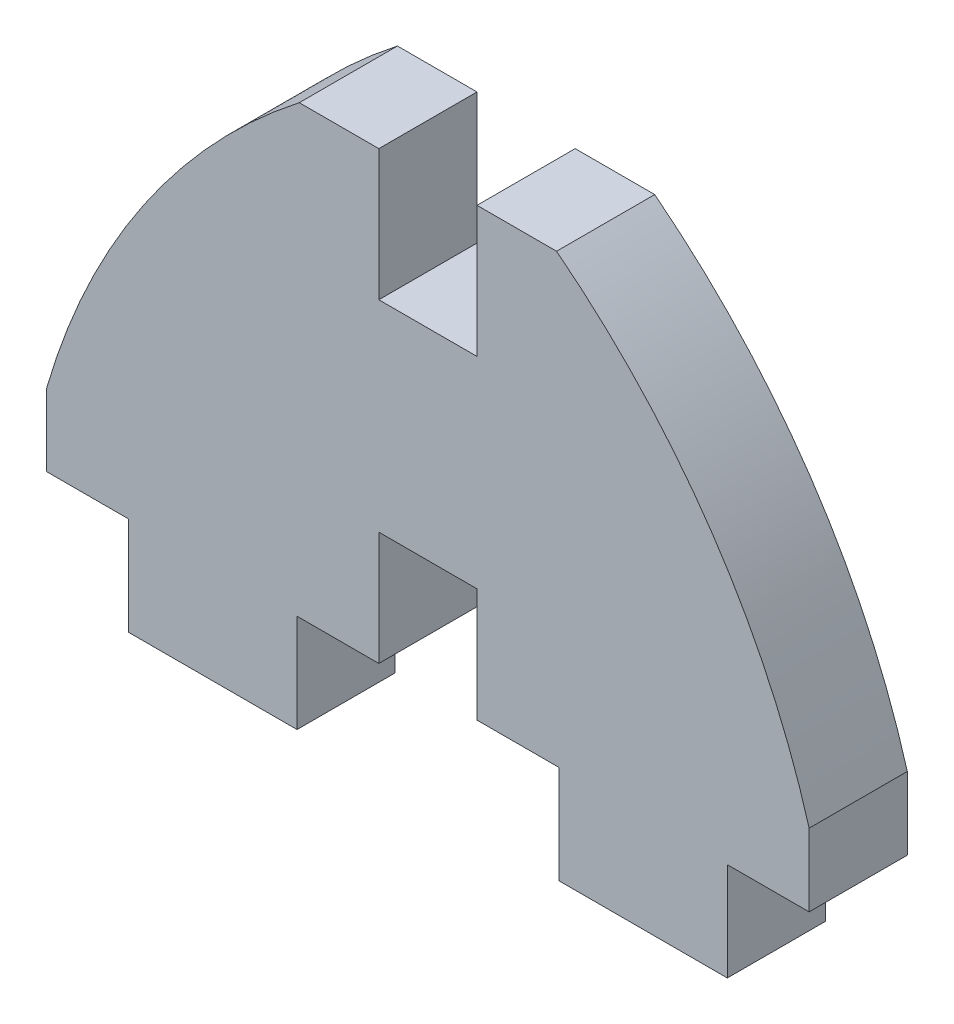
SolidWorks part; units mm, degrees
ref_plane "Front Plane" through (0, 0, 0) normal (0, 0, 1) x (1, 0, 0)
ref_plane "Top Plane" through (0, 0, 0) normal (0, 1, 0) x (1, 0, 0)
ref_plane "Right Plane" through (0, 0, 0) normal (1, 0, 0) x (0, 0, -1)
sketch "Sketch1" plane through (0, 0, 0) normal (0, 0, 1) x (1, 0, 0)
  line L0 (3, 0) -> (-3, 0)
  line L1 (-3, 0) -> (-3, -6.95)
  line L2 (-3, -6.95) -> (-8, -6.95)
  line L3 (-8, -6.95) -> (-8, -12.95)
  line L4 (-8, -12.95) -> (-18.3, -12.95)
  line L5 (-18.3, -12.95) -> (-18.3, -6.95)
  line L6 (-18.3, -6.95) -> (-23.3, -6.95)
  line L7 (-23.3, -6.95) -> (-23.3, -2.5185)
  line L8 (0, 0) -> (0, 12.2963) construction
  line L9 (3, 12.3) -> (-3, 12.3)
  line L10 (-3, 12.3) -> (-3, 20.3)
  line L11 (-3, 20.3) -> (-7.8633, 20.3)
  line L12 (23.3, -6.95) -> (23.3, -2.5185)
  line L13 (18.3, -6.95) -> (23.3, -6.95)
  line L14 (18.3, -12.95) -> (18.3, -6.95)
  line L15 (8, -6.95) -> (8, -12.95)
  line L16 (8, -12.95) -> (18.3, -12.95)
  line L17 (3, -6.95) -> (8, -6.95)
  line L18 (3, 0) -> (3, -6.95)
  line L19 (3, 12.3) -> (3, 20.3)
  line L20 (3, 20.3) -> (7.8633, 20.3)
  arc A0 (-23.3, -2.5185) -> (-7.8633, 20.3) centre (19.5786, -14.8952) cw
  arc A1 (23.3, -2.5185) -> (7.8633, 20.3) centre (-19.5786, -14.8952) ccw
  point P25 (0, 12.3)
  dimension "D1" = 3
  dimension "D2" = 6.95
  dimension "D3" = 10.3
  dimension "D4" = 5
  dimension "D5" = 5
  dimension "D6" = 12.3
  dimension "D7" = 6
  dimension "D8" = 6
  dimension "D9" = 8
extrude "Boss-Extrude1" add sketch "Sketch1" along normal blind 6 contours A0 L11 L10 L9 L19 L20 A1 L12 L13 L14 L16 L15 L17 L18 L0 L1 L2 L3 L4 L5 L6 L7
